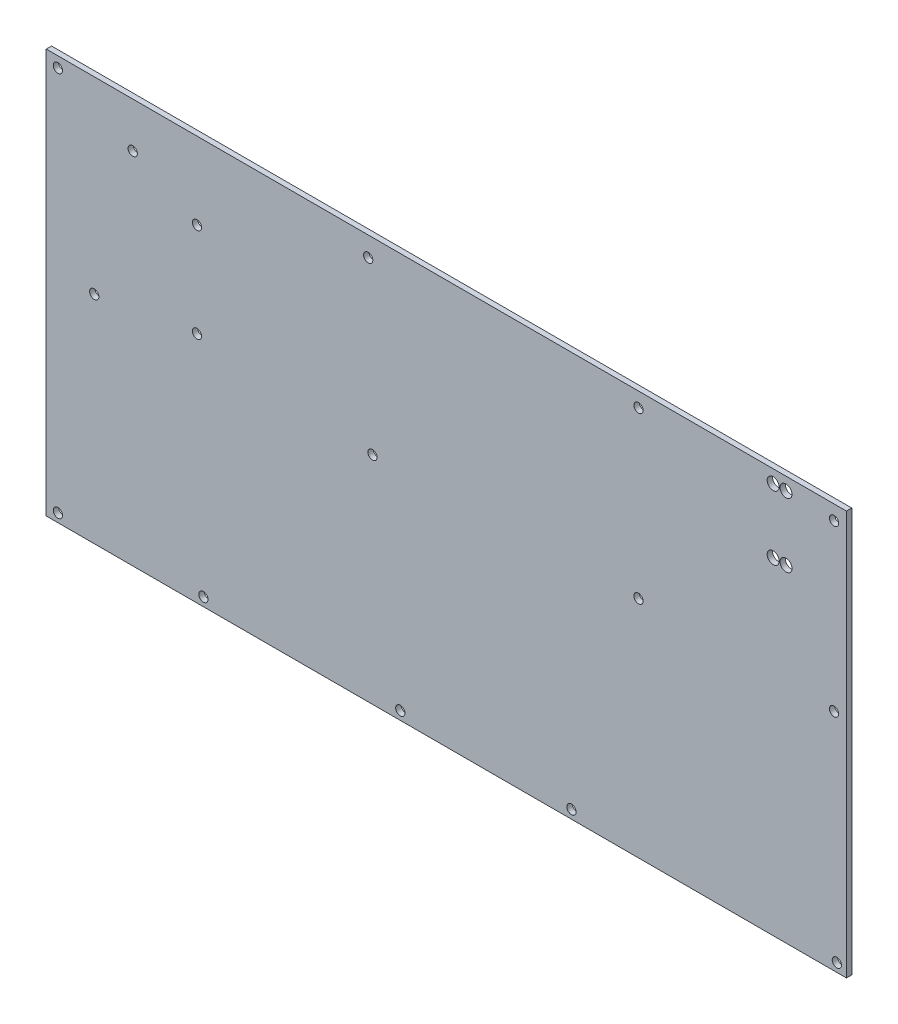
SolidWorks part; units mm, degrees
ref_plane "Front Plane" through (0, 0, 0) normal (0, 0, 1) x (1, 0, 0)
ref_plane "Top Plane" through (0, 0, 0) normal (0, 1, 0) x (1, 0, 0)
ref_plane "Right Plane" through (0, 0, 0) normal (1, 0, 0) x (0, 0, -1)
sketch "Sketch1" plane through (0, 0, 0) normal (0, 0, 1) x (1, 0, 0)
  line L0 (-51.1882, 19.6128) -> (-39.9222, 19.6128) construction
  line L1 (-39.9222, -40.382) -> (197.517, -40.382)
  line L2 (-39.9222, -40.382) -> (-39.9222, 79.6076)
  line L3 (-39.9222, 79.6076) -> (197.517, 79.6076)
  line L4 (197.517, -40.382) -> (197.517, 79.6076)
  line L5 (-51.1882, 26.9589) -> (-51.1882, 12.2667) construction
  line L6 (152.1018, -60.4872) -> (152.1018, -45.4872) construction
  circle A0 centre (193.834, 75.2896) radius 1.3716
  circle A1 centre (135.8154, 75.2896) radius 1.3716
  circle A2 centre (193.834, 26.293) radius 1.3716
  circle A3 centre (135.8204, 26.293) radius 1.3716
  circle A4 centre (194.6722, -37.842) radius 1.3716
  circle A5 centre (115.9322, -37.842) radius 1.3716
  circle A6 centre (55.6072, 73.791) radius 1.3716
  circle A7 centre (56.8772, 23.753) radius 1.3716
  circle A8 centre (65.1322, -37.842) radius 1.3716
  circle A9 centre (4.8072, 56.773) radius 1.3716
  circle A10 centre (4.8072, 28.833) radius 1.3716
  circle A11 centre (6.7122, -37.842) radius 1.3716
  circle A12 centre (-14.2718, 66.2672) radius 1.3716
  circle A13 centre (-36.4678, 76.4834) radius 1.3716
  circle A14 centre (-25.6728, 23.753) radius 1.3716
  circle A15 centre (-36.4678, -37.842) radius 1.3716
  circle A16 centre (179.5846, 75.823) radius 1.778
  circle A17 centre (175.7746, 75.7976) radius 1.778
  circle A18 centre (179.5846, 56.7476) radius 1.778
  circle A19 centre (175.7746, 56.7476) radius 1.778
  point P9 (-39.9222, 19.6128)
  point P59 (181.3626, 56.7476)
  point P60 (179.5846, 54.9696)
  point P61 (177.392, 53.7879)
  point P62 (175.7746, 54.9696)
  point P63 (172.7937, 57.8272)
  point P64 (173.9966, 56.7476)
  dimension "D6" = 2.7432
  dimension "D8" = 2.7432
  dimension "D10" = 2.7432
  dimension "D13" = 2.7432
  dimension "D16" = 2.7432
  dimension "D19" = 2.7432
  dimension "D22" = 2.7432
  dimension "D25" = 2.7432
  dimension "D28" = 2.7432
  dimension "D31" = 2.7432
  dimension "D34" = 2.7432
  dimension "D37" = 2.7432
  dimension "D40" = 2.7432
  dimension "D42" = 2.7432
  dimension "D45" = 2.7432
  dimension "D48" = 2.7432
  dimension "D51" = 3.556
  dimension "D54" = 3.556
  dimension "D57" = 3.556
  dimension "D60" = 3.556
  dimension "D1" = 119.9896
  dimension "D2" = 237.4392
  dimension "D3" = 45.4152
  dimension "D4" = 3.683
  dimension "D5" = 4.318
  dimension "D7" = 61.7017
  dimension "D9" = 4.318
  dimension "D11" = 3.683
  dimension "D12" = 53.3146
  dimension "D14" = 61.6966
  dimension "D15" = 53.3146
  dimension "D17" = 2.8448
  dimension "D18" = 117.4496
  dimension "D20" = 81.5848
  dimension "D21" = 117.4496
  dimension "D23" = 141.9098
  dimension "D24" = 5.8166
  dimension "D26" = 140.6398
  dimension "D27" = 55.8546
  dimension "D29" = 132.3848
  dimension "D30" = 117.4496
  dimension "D32" = 192.7098
  dimension "D33" = 22.8346
  dimension "D35" = 192.7098
  dimension "D36" = 50.7746
  dimension "D38" = 190.8048
  dimension "D39" = 117.4496
  dimension "D41" = 211.7888
  dimension "D43" = 233.9848
  dimension "D44" = 3.1242
  dimension "D46" = 223.1898
  dimension "D47" = 55.8546
  dimension "D49" = 233.9848
  dimension "D50" = 117.4496
  dimension "D52" = 17.9324
  dimension "D53" = 3.7846
  dimension "D55" = 21.7424
  dimension "D56" = 3.81
  dimension "D58" = 17.9324
  dimension "D59" = 22.86
  dimension "D61" = 22.86
  dimension "D62" = 21.7424
extrude "Boss-Extrude1" add sketch "Sketch1" along normal blind 1.5748 from offset 6
